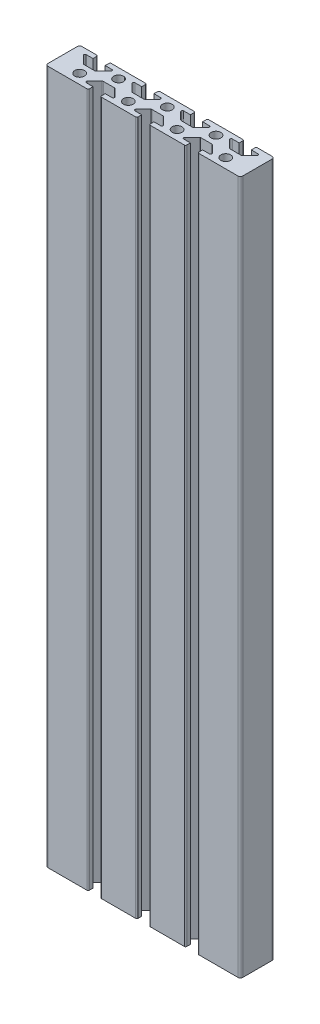
SolidWorks part; units mm, degrees
ref_plane "Front Plane" through (0, 0, 0) normal (0, 0, 1) x (1, 0, 0)
ref_plane "Top Plane" through (0, 0, 0) normal (0, 1, 0) x (1, 0, 0)
ref_plane "Right Plane" through (0, 0, 0) normal (1, 0, 0) x (0, 0, -1)
sketch "Sketch1" plane through (0, 0, 0) normal (0, 1, 0) x (1, 0, 0)
  line L0 (63.5, 12) -> (67.5, 12)
  line L1 (0, 0) -> (80, 0)
  line L2 (0, 0) -> (0, 14)
  line L3 (0, 14) -> (80, 14)
  line L4 (80, 0) -> (80, 14)
  line L5 (67.5, 12) -> (67.5, 14)
  line L6 (67.5, 14) -> (72.5, 14)
  line L7 (72.5, 14) -> (72.5, 12)
  line L9 (76.5, 12) -> (72.5, 8)
  line L10 (72.5, 8) -> (67.5, 8)
  line L11 (67.5, 8) -> (63.5, 12)
  line L12 (72.5, 12) -> (76.5, 12)
  line L13 (52.5, 12) -> (56.5, 12)
  line L14 (56.5, 12) -> (52.5, 8)
  line L15 (52.5, 8) -> (47.5, 8)
  line L16 (47.5, 8) -> (43.5, 12)
  line L17 (43.5, 12) -> (47.5, 12)
  line L18 (47.5, 12) -> (47.5, 14)
  line L19 (47.5, 14) -> (52.5, 14)
  line L20 (52.5, 14) -> (52.5, 12)
  line L21 (32.5, 12) -> (36.5, 12)
  line L22 (36.5, 12) -> (32.5, 8)
  line L23 (32.5, 8) -> (27.5, 8)
  line L24 (27.5, 8) -> (23.5, 12)
  line L25 (23.5, 12) -> (27.5, 12)
  line L26 (27.5, 12) -> (27.5, 14)
  line L27 (27.5, 14) -> (32.5, 14)
  line L28 (32.5, 14) -> (32.5, 12)
  line L29 (12.5, 12) -> (16.5, 12)
  line L30 (16.5, 12) -> (12.5, 8)
  line L31 (12.5, 8) -> (7.5, 8)
  line L32 (7.5, 8) -> (3.5, 12)
  line L33 (3.5, 12) -> (7.5, 12)
  line L34 (7.5, 12) -> (7.5, 14)
  line L35 (7.5, 14) -> (12.5, 14)
  line L36 (12.5, 14) -> (12.5, 12)
  line L37 (57.5, 0) -> (57.5, 2)
  line L38 (57.5, 2) -> (53.5, 2)
  line L39 (53.5, 2) -> (57.5, 6)
  line L40 (57.5, 6) -> (62.5, 6)
  line L41 (62.5, 6) -> (66.5, 2)
  line L42 (66.5, 2) -> (62.5, 2)
  line L43 (62.5, 2) -> (62.5, 0)
  line L44 (62.5, 0) -> (57.5, 0)
  line L45 (42.5, 0) -> (37.5, 0)
  line L46 (37.5, 0) -> (37.5, 2)
  line L47 (37.5, 2) -> (33.5, 2)
  line L48 (33.5, 2) -> (37.5, 6)
  line L49 (37.5, 6) -> (42.5, 6)
  line L50 (42.5, 6) -> (46.5, 2)
  line L51 (46.5, 2) -> (42.5, 2)
  line L52 (42.5, 2) -> (42.5, 0)
  line L53 (22.5, 0) -> (17.5, 0)
  line L54 (17.5, 0) -> (17.5, 2)
  line L55 (17.5, 2) -> (13.5, 2)
  line L56 (13.5, 2) -> (17.5, 6)
  line L57 (17.5, 6) -> (22.5, 6)
  line L58 (22.5, 6) -> (26.5, 2)
  line L59 (26.5, 2) -> (22.5, 2)
  line L60 (22.5, 2) -> (22.5, 0)
  circle A0 centre (60, 10) radius 2
  circle A1 centre (40, 10) radius 2
  circle A2 centre (20, 10) radius 2
  circle A3 centre (70, 4) radius 2
  circle A4 centre (50, 4) radius 2
  circle A5 centre (30, 4) radius 2
  circle A6 centre (10, 4) radius 2
  dimension "D17" = 4
  dimension "D21" = 4
  dimension "D1" = 80
  dimension "D2" = 14
  dimension "D3" = 7.5
  dimension "D4" = 5
  dimension "D5" = 6
  dimension "D6" = 17.5
  dimension "D7" = 2
  dimension "D8" = 4
  dimension "D9" = 5
  dimension "D10" = 5
  dimension "D11" = 4
  dimension "D12" = 4
  dimension "D13" = 2
  dimension "D14" = 2
  dimension "D15" = 6
  dimension "D16" = 3
  dimension "D18" = 20
  dimension "D19" = 4
  dimension "D22" = 10
  dimension "D23" = 4
  dimension "D20" = 3
  dimension "D24" = 4
extrude "Boss-Extrude1" add sketch "Sketch1" along normal blind 285 contours L59 L60 L1 L46 L47 L48 L49 L50 L51 L52 L37 L38 L39 L40 L41 L42 L43 L4 L3 L7 L12 L9 L10 L11 L0 L5 L20 L13 L14 L15 L16 L17 L18 L28 L21 L22 L23 L24 L25 L26 L36 L29 L30 L31 L32 L33
fillet "Fillet1" radius 0.5 24 edges at (67.5, 142.5, -8) (63.5, 142.5, -12) (76.5, 142.5, -12) (72.5, 142.5, -8) (47.5, 142.5, -8) (27.5, 142.5, -8) (52.5, 142.5, -8) (32.5, 142.5, -8) (56.5, 142.5, -12) (36.5, 142.5, -12) (43.5, 142.5, -12) (23.5, 142.5, -12) (12.5, 142.5, -8) (7.5, 142.5, -8) (3.5, 142.5, -12) (16.5, 142.5, -12) (72.5, 142.5, -14) (67.5, 142.5, -14) (52.5, 142.5, -14) (47.5, 142.5, -14) (32.5, 142.5, -14) (27.5, 142.5, -14) (12.5, 142.5, -14) (7.5, 142.5, -14)
fillet "Fillet2" radius 0.5 18 edges at (17.5, 142.5, -6) (26.5, 142.5, -2) (22.5, 142.5, -6) (22.5, 142.5, 0) (17.5, 142.5, 0) (13.5, 142.5, -2) (33.5, 142.5, -2) (37.5, 142.5, -6) (42.5, 142.5, -6) (42.5, 142.5, 0) (46.5, 142.5, -2) (37.5, 142.5, 0) (57.5, 142.5, 0) (62.5, 142.5, 0) (53.5, 142.5, -2) (57.5, 142.5, -6) (66.5, 142.5, -2) (62.5, 142.5, -6)
fillet "Fillet3" radius 1 4 edges at (0, 142.5, -14) (0, 142.5, 0) (80, 142.5, -14) (80, 142.5, 0)
sketch "Sketch2" plane through (0, 0, -14) normal (0, 0, -1) x (-1, 0, 0)
  line L0 (-33, 0) -> (-47, 0) construction
  circle A1 centre (-40, 10) radius 2.5
  dimension "D1" = 10
  dimension "D2" = 5
extrude "Cut-Extrude2" cut sketch "Sketch2" against normal blind 230 contours A1
sketch "Sketch3" plane through (0, 0, -14) normal (0, 0, -1) x (-1, 0, 0)
  circle A0 centre (-40, 10) radius 5.5
  dimension "D1" = 11
extrude "Cut-Extrude3" cut sketch "Sketch3" against normal blind 7 contours A0
sketch "Sketch4" plane through (0, 0, -14) normal (0, 0, -1) x (-1, 0, 0)
  line L0 (-33, 285) -> (-47, 285) construction
  circle A0 centre (-40, 275) radius 2.5
  dimension "D1" = 5
  dimension "D2" = 10
extrude "Cut-Extrude4" cut sketch "Sketch4" against normal blind 7
sketch "Sketch5" plane through (0, 0, -14) normal (0, 0, -1) x (-1, 0, 0)
  circle A0 centre (-40, 275) radius 5.5
  dimension "D1" = 11
extrude "Cut-Extrude5" cut sketch "Sketch5" against normal blind 7
